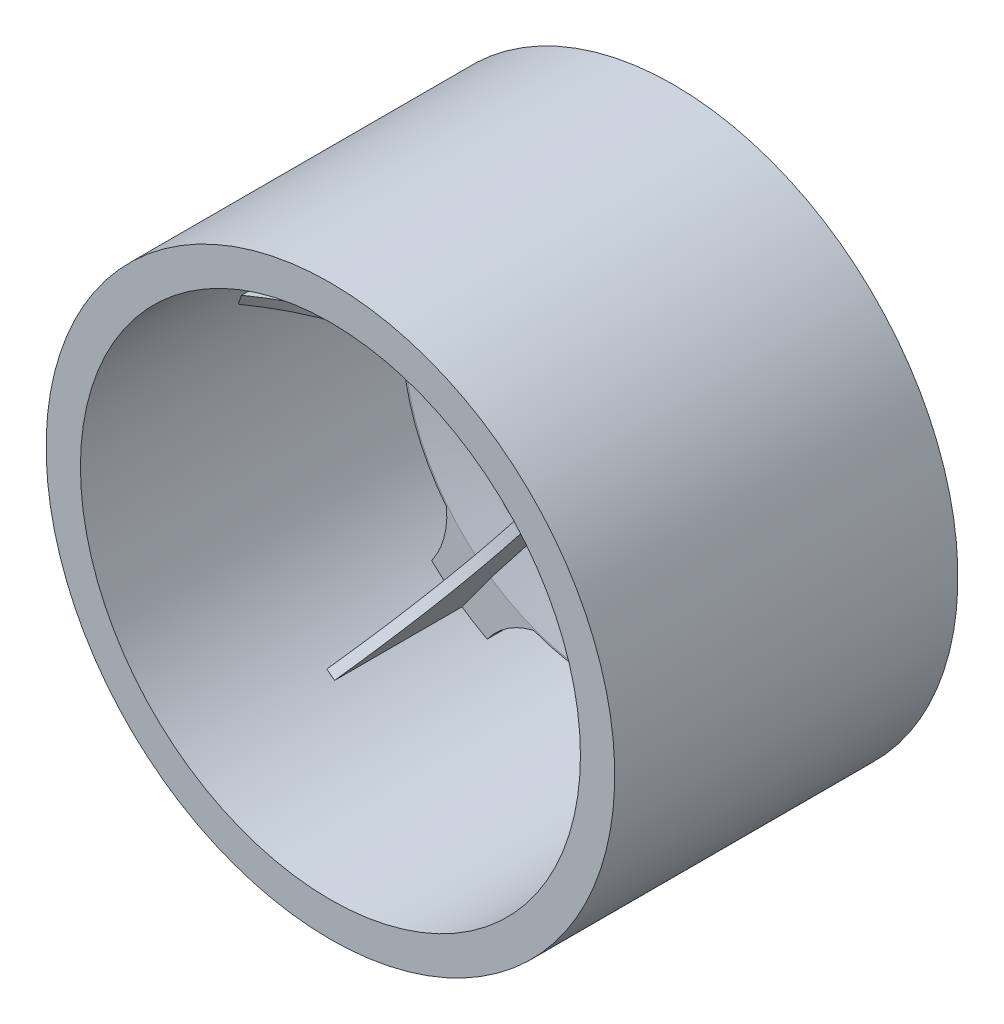
SolidWorks part; units mm, degrees
material "Plastique personnalisé"
ref_plane "Plan de face" through (0, 0, 0) normal (0, 0, 1) x (1, 0, 0)
ref_plane "Plan de dessus" through (0, 0, 0) normal (0, 1, 0) x (1, 0, 0)
ref_plane "Plan de droite" through (0, 0, 0) normal (1, 0, 0) x (0, 0, -1)
sketch "Esquisse1" plane through (0, 0, 0) normal (1, 0, 0) x (0, 0, -1)
  line L0 (0, 0) -> (-4, 0)
  line L1 (-4, 0) -> (-4, 8.5)
  line L2 (-4, 8.5) -> (-1, 8.5)
  line L3 (-1, 8.5) -> (1.5, 13.5)
  line L4 (1.5, 13.5) -> (0, 20.5)
  line L5 (0, 20.5) -> (0, 25.5)
  line L6 (0, 25.5) -> (-28, 25.5)
  line L7 (-28, 25.5) -> (-28, 29)
  line L8 (-28, 29) -> (7, 29)
  line L9 (7, 29) -> (7, 25.5)
  line L10 (7, 25.5) -> (1.5, 25.5)
  line L11 (1.5, 25.5) -> (1.5, 20.6589)
  line L14 (4.4269, 7) -> (4.4269, 5)
  line L15 (4.4269, 5) -> (1.4269, 5)
  line L16 (1.4269, 5) -> (1.4269, 0)
  line L17 (1.4269, 0) -> (0, 0)
  line L18 (1.5, 20.6589) -> (3.2181, 12.6409)
  line L19 (3.2181, 12.6409) -> (1.673, 9.5507)
  line L20 (1.673, 9.5507) -> (4.4269, 7)
  dimension "D1" = 35
  dimension "D2" = 24
  dimension "D3" = 3
  dimension "D4" = 5
  dimension "D5" = 2.5
  dimension "D6" = 28
  dimension "D7" = 7
  dimension "D8" = 8.5
  dimension "D9" = 29
  dimension "D10" = 3.5
  dimension "D11" = 1.5
  dimension "D12" = 2
  dimension "D13" = 5
  dimension "D14" = 3
revolve "Révolution1" add sketch "Esquisse1" angle 360 about L0
sketch "Esquisse3" plane through (0, 0, 0) normal (1, 0, 0) x (0, 0, -1)
  line L1 (-1, 8.5) -> (-1, -8.5) construction
  line L4 (4.4269, -7) -> (4.4269, 7) construction
  line L11 (-28, 29) -> (-28, -29) construction
  line L12 (-28, 25.5) -> (-28, -25.5) construction
  line L15 (-1, 8.5) -> (-3, 8.5)
  line L16 (4.4269, 7) -> (3.2181, 12.6409)
  line L17 (3.2181, 12.6409) -> (1.673, 9.5507)
  line L18 (1.673, 9.5507) -> (4.4269, 7)
  line L19 (-1, 8.5) -> (1.5, 13.5)
  line L20 (1.5, 13.5) -> (0, 20.5)
  line L21 (0, 20.5) -> (0, 25.5)
  line L22 (0, 25.5) -> (-13, 25.5)
  line L23 (-4, 8.5) -> (-1, 8.5) construction
  spline S0 degree 2 poles (-3, 8.5) (-4.6871, 18.606) (-13, 25.5) knots 0 0 0 1 1 1
  dimension "D1" = 13
  dimension "D2" = 11.5
  dimension "D3" = 7
  dimension "D4" = 2
  dimension "D5" = 15
  dimension "D6" = 23.5
extrude "Boss.-Extru.3" add sketch "Esquisse3" along normal mid plane 1 separate body
sketch "Esquisse4" plane through (0, 0, -1.5) normal (0, 0, -1) x (-1, 0, 0)
  line L0 (0, 0) -> (0, 29) construction
  line L1 (0, 0) -> (-17.0458, 23.4615) construction
  circle A0 centre (0, 0) radius 29 construction
  circle A1 centre (0, 0) radius 20.6589 construction
  circle A2 centre (0, 0) radius 25.5 construction
  arc A3 (-3.5, 25.2587) -> (-22.9409, 11.1341) centre (0, 0) ccw
  arc A4 (-5.5, 19.9133) -> (-17.2391, 11.3844) centre (0, 0) ccw
  spline S0 degree 2 poles (-5.5, 19.9133) (-3.5484, 22.1923) (-3.5, 25.2587) knots 0 0 0 1 1 1
  spline S1 degree 2 poles (-17.2391, 11.3844) (-20.0096, 10.2326) (-22.9409, 11.1341) knots 0 0 0 1 1 1
  dimension "D4" = 4.231
  dimension "D1" = 5.5
  dimension "D2" = 3.5
  dimension "D3" = 36
  dimension "D5" = 1.976
extrude "Enlèv. mat.-Extru.1" cut sketch "Esquisse4" against normal up to next (1.5 mm away)
pattern_circular "Répétition circulaire3" count 5 over 360 about axis through (0, 0, 0) along (0, 0, -1) of "Enlèv. mat.-Extru.1"
pattern_circular "Répétition circulaire14" count 5 over 360 about axis through (0, 0, 0) along (0, 0, -1) of bodies 109 110
sketch "Esquisse6" plane through (0, 0, 4) normal (0, 0, 1) x (1, 0, 0)
  line L0 (0, 0) -> (6.9282, 0) construction
  line L1 (3.4641, 6) -> (-3.4641, 6)
  line L2 (-3.4641, 6) -> (-6.9282, 0)
  line L3 (-6.9282, 0) -> (-3.4641, -6)
  line L4 (-3.4641, -6) -> (3.4641, -6)
  line L5 (3.4641, -6) -> (6.9282, 0)
  line L6 (6.9282, 0) -> (3.4641, 6)
  circle A0 centre (0, 0) radius 6 construction
  dimension "D1" = 6
extrude "Enlèv. mat.-Extru.2" cut sketch "Esquisse6" against normal blind 4
sketch "Esquisse7" plane through (0, 0, -1.4269) normal (0, 0, -1) x (-1, 0, 0)
  circle A0 centre (0, 0) radius 1.5
  dimension "D1" = 3
extrude "Enlèv. mat.-Extru.3" cut sketch "Esquisse7" against normal up to next
